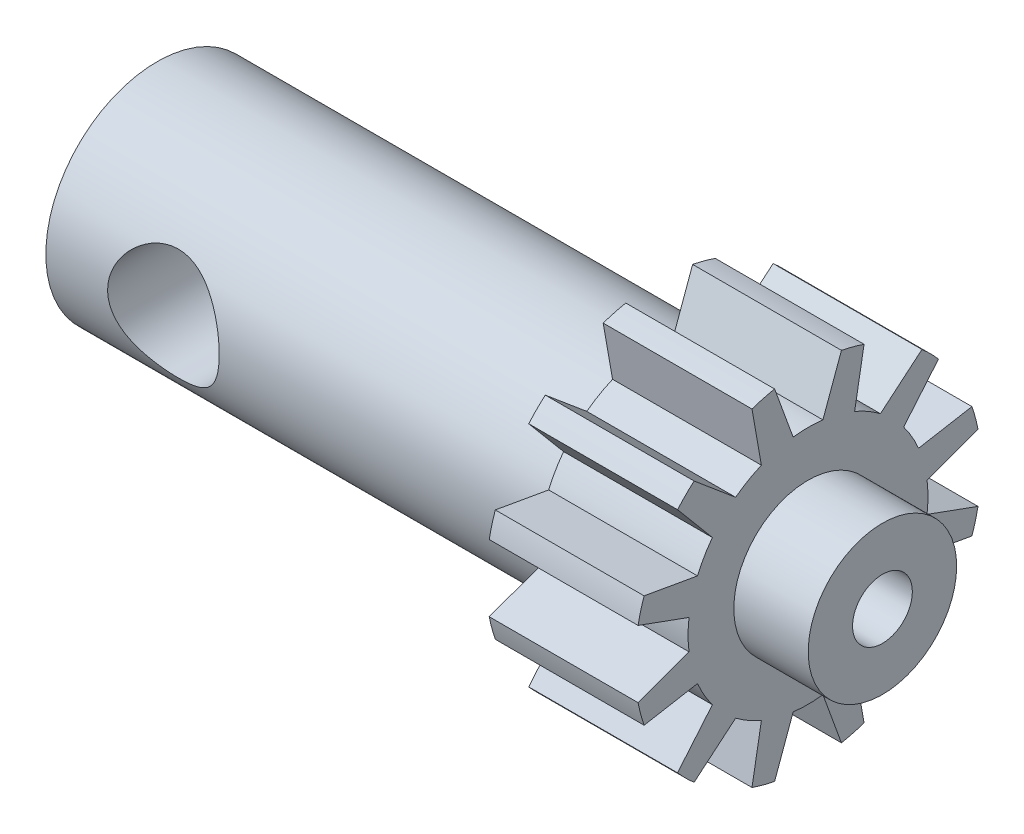
SolidWorks part; units mm, degrees
ref_plane "Front Plane" through (0, 0, 0) normal (0, 0, 1) x (1, 0, 0)
ref_plane "Top Plane" through (0, 0, 0) normal (0, 1, 0) x (1, 0, 0)
ref_plane "Right Plane" through (0, 0, 0) normal (1, 0, 0) x (0, 0, -1)
sketch "Sketch1" plane through (0, 0, 0) normal (0, 0, 1) x (1, 0, 0)
  line L0 (0, 0) -> (-81.3138, 0) construction
  line L1 (0, 0) -> (0, 9.4932)
  line L2 (0, 9.4932) -> (42.8498, 9.4932)
  line L3 (42.8498, 9.4932) -> (42.8498, 14.7828)
  line L4 (42.8498, 14.7828) -> (55.5498, 14.7828)
  line L5 (55.5498, 14.7828) -> (55.5498, 6.3348)
  line L6 (55.5498, 6.3348) -> (61.8998, 6.3348)
  line L7 (61.8998, 6.3348) -> (61.8998, 0)
  line L8 (61.8998, 0) -> (0, 0)
  dimension "D1" = 61.8998
  dimension "D2" = 18.9865
  dimension "D3" = 12.7
  dimension "D4" = 6.35
  dimension "D5" = 29.5656
  dimension "D6" = 12.6695
revolve "Revolve1" add sketch "Sketch1" angle 360 about L0
hole_wizard "Hole1" positions "3DSketch4" profile "Sketch8" legacy end condition through all
sketch3d "3DSketch4"
  line L0 (0, 0, 0) -> (0, 0, 9.4932) construction
  circle A0 centre (0, 0, 0) radius 9.4932 construction
  point P0 (10.033, 0, 9.4932)
  point P8 (9.4932, 0, 0)
  dimension "D1" = 10.033
sketch "Sketch8" plane through (10.033, 0, 9.4932) normal (1, 0, 0) x (0, -1, 0)
  line L0 (0, 0) -> (0, 24.2761)
  line L1 (0, 24.2761) -> (4.7625, 24.2761)
  line L2 (4.7625, 24.2761) -> (4.7625, 0)
  line L3 (4.7625, 0) -> (0, 0)
  line L4 (0, 110) -> (0, -10) construction
  dimension "Diameter" = 9.525
  dimension "Depth" = 24.2761
hole_wizard "1/4-20 Tapped Hole1" positions "Sketch11" profile "Sketch12" tap size "1/4-20" standard "ANSI Inch"
sketch "Sketch11" plane through (61.8998, 0, 0) normal (1, 0, 0) x (0, 0, -1)
  point P0 (0, 0)
sketch "Sketch12" plane through (61.8998, 0, 0) normal (0, 1, 0) x (0, 0, -1)
  line L0 (0, 0) -> (0, 18.0438)
  line L1 (0, 18.0438) -> (2.5527, 16.51)
  line L2 (2.5527, 16.51) -> (2.5527, 0)
  line L5 (2.5527, 0) -> (0, 0)
  line L10 (0, 18.0438) -> (-2.5527, 16.51) construction
  line L11 (0, -6.35) -> (0, 107.95) construction
  dimension "Tap Drill Dia." = 5.1054
  dimension "Tap Drill Depth" = 16.51
  dimension "Drill Angle" = 118
cosmetic thread "Hole Thread1" parameters "D1"=10.16, "D2"=6.35
sketch "Sketch13" plane through (55.5498, 0, 0) normal (1, 0, 0) x (0, 0, -1)
  line L0 (0, 0) -> (0, 18.4028) construction
  line L1 (-1.27, 10.1571) -> (-2.8525, 14.505)
  line L2 (1.27, 10.1571) -> (2.8525, 14.505)
  arc A0 (1.27, 10.1571) -> (-1.27, 10.1571) centre (0, 0) ccw
  circle A1 centre (0, 0) radius 14.7828 construction
  dimension "D3" = 20.4724
  dimension "D1" = 40
  dimension "D2" = 2.54
extrude "Cut-Extrude1" cut sketch "Sketch13" against normal through all both and the other way through all
pattern_circular "CirPattern1" count 12 over 360 about axis through (55.5498, 0, 0) along (1, 0, 0) of "Cut-Extrude1"
